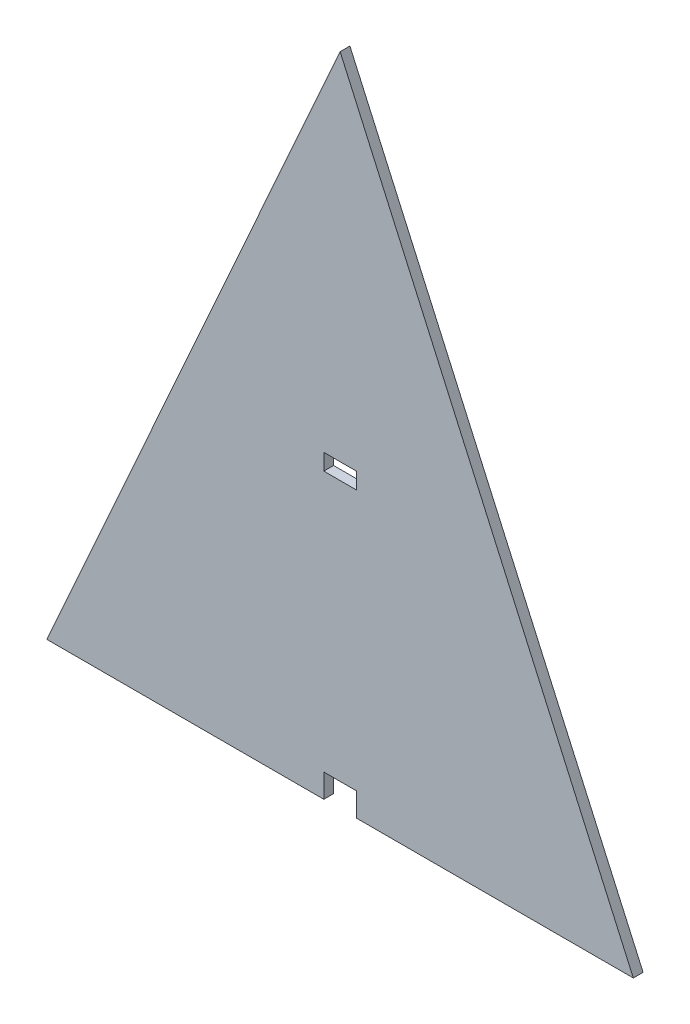
SolidWorks part; units mm, degrees
ref_plane "Front Plane" through (0, 0, 0) normal (0, 0, 1) x (1, 0, 0)
ref_plane "Top Plane" through (0, 0, 0) normal (0, 1, 0) x (1, 0, 0)
ref_plane "Right Plane" through (0, 0, 0) normal (1, 0, 0) x (0, 0, -1)
sketch "Sketch1" plane through (0, 0, 0) normal (0, 0, 1) x (1, 0, 0)
  line L0 (0, 0) -> (180, 0)
  line L1 (180, 0) -> (90, 201.25)
  line L2 (90, 201.25) -> (0, 0)
  line L3 (90, 201.25) -> (90, 0) construction
  line L4 (3.2467, 7.26) -> (176.7533, 7.26) construction
  line L5 (40, 89.4444) -> (140, 89.4444) construction
  line L6 (85, 7.26) -> (95, 7.26)
  line L7 (85, 7.26) -> (85, 0)
  line L8 (85, 0) -> (95, 0)
  line L9 (95, 7.26) -> (95, 0)
  line L10 (41.249, 92.2374) -> (138.751, 92.2374) construction
  line L12 (95, 92.2374) -> (85, 92.2374)
  line L13 (95, 92.2374) -> (95, 87.2374)
  line L14 (95, 87.2374) -> (85, 87.2374)
  line L15 (85, 92.2374) -> (85, 87.2374)
  dimension "D1" = 180
  dimension "D2" = 201.25
  dimension "D3" = 193.99
  dimension "D4" = 10
  dimension "D5" = 5
  dimension "D6" = 100
  dimension "D7" = 10
  dimension "D8" = 5
  dimension "D9" = 5
  dimension "D10" = 2.793
extrude "Boss-Extrude1" add sketch "Sketch1" along normal blind 3 contours L6 L9 L0 L1 L2 L7 L12 L15 L14 L13
